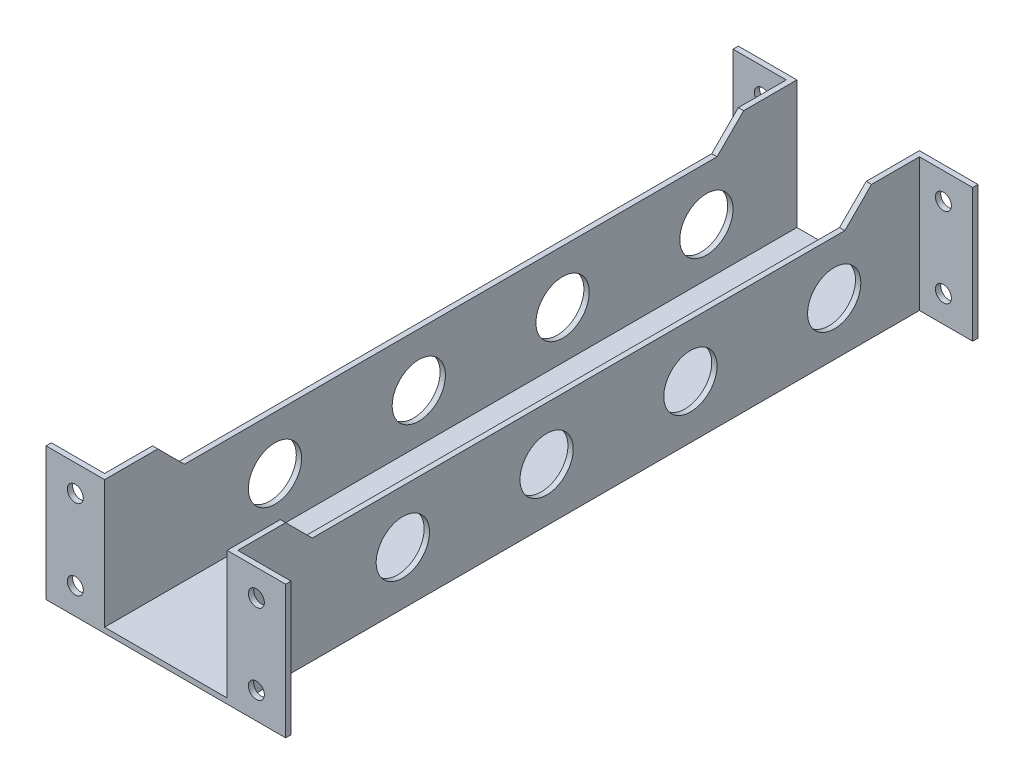
SolidWorks part; units mm, degrees
material "1060 Alloy"
ref_plane "Front Plane" through (0, 0, 0) normal (0, 0, 1) x (1, 0, 0)
ref_plane "Top Plane" through (0, 0, 0) normal (0, 1, 0) x (1, 0, 0)
ref_plane "Right Plane" through (0, 0, 0) normal (1, 0, 0) x (0, 0, -1)
sketch "Sketch1" plane through (0, 0, 0) normal (0, 1, 0) x (1, 0, 0)
  line L1 (-12.5, -65) -> (12.5, -65)
  line L2 (-12.5, -65) -> (-12.5, 65)
  line L3 (-12.5, 65) -> (12.5, 65)
  line L4 (12.5, -65) -> (12.5, 65)
  line L5 (-12.5, -65) -> (12.5, 65) construction
  line L6 (-12.5, 65) -> (12.5, -65) construction
  point P0 (0, 0)
  dimension "D1" = 130
  dimension "D2" = 25
extrude "Boss-Extrude1" add sketch "Sketch1" along normal blind 1
sketch "Sketch2" plane through (0, 1, 0) normal (0, 1, 0) x (1, 0, 0)
  line L0 (-12.5, -65) -> (12.5, -65) construction
  line L1 (12.5, 65) -> (11.5, 65)
  line L2 (12.5, 65) -> (12.5, -65)
  line L3 (12.5, -65) -> (11.5, -65)
  line L4 (11.5, 65) -> (11.5, -65)
  line L6 (-12.5, 65) -> (-11.5, 65)
  line L7 (-12.5, 65) -> (-12.5, -65)
  line L8 (-12.5, -65) -> (-11.5, -65)
  line L9 (-11.5, 65) -> (-11.5, -65)
  dimension "D1" = 1
  dimension "D2" = 1
extrude "Boss-Extrude2" add sketch "Sketch2" along normal blind 24
sketch "Sketch3" plane through (12.5, 0, 0) normal (1, 0, 0) x (0, 0, -1)
  line L0 (-65, 0) -> (65, 0) construction
  line L1 (-65, 25) -> (-64, 25)
  line L2 (-65, 25) -> (-65, 0)
  line L3 (-65, 0) -> (-64, 0)
  line L4 (-64, 25) -> (-64, 0)
  line L6 (65, 25) -> (64, 25)
  line L7 (65, 25) -> (65, 0)
  line L8 (65, 0) -> (64, 0)
  line L9 (64, 25) -> (64, 0)
  dimension "D1" = 1
  dimension "D2" = 1
extrude "Boss-Extrude3" add sketch "Sketch3" along normal blind 10
sketch "Sketch4" plane through (-12.5, 0, 0) normal (-1, 0, 0) x (0, 0, 1)
  line L0 (-65, 0) -> (65, 0) construction
  line L1 (-65, 25) -> (-64, 25)
  line L2 (-65, 25) -> (-65, 0)
  line L3 (-65, 0) -> (-64, 0)
  line L4 (-64, 25) -> (-64, 0)
  line L6 (65, 25) -> (64, 25)
  line L7 (65, 25) -> (65, 0)
  line L8 (65, 0) -> (64, 0)
  line L9 (64, 25) -> (64, 0)
  dimension "D1" = 1
  dimension "D2" = 1
extrude "Boss-Extrude4" add sketch "Sketch4" along normal blind 10
sketch "Sketch5" plane through (0, 1, 0) normal (0, 1, 0) x (1, 0, 0)
  line L0 (0, -65) -> (0, -38)
  line L1 (-11.5, -65) -> (11.5, -65) construction
  line L2 (0, -38) -> (0, -33)
  line L3 (0, -28) -> (0, -11)
  line L4 (0, -11) -> (0, -6)
  line L5 (0, -1) -> (0, 16)
  line L6 (0, 16) -> (0, 21)
  line L7 (0, 26) -> (0, 43)
  line L8 (0, 43) -> (0, 48)
  circle A0 centre (0, -33) radius 5
  circle A1 centre (0, -6) radius 5
  circle A2 centre (0, 21) radius 5
  circle A3 centre (0, 48) radius 5
  dimension "D1" = 27
  dimension "D2" = 5
  dimension "D3" = 17
  dimension "D4" = 5
  dimension "D5" = 17
  dimension "D6" = 5
  dimension "D7" = 17
  dimension "D8" = 5
extrude "Cut-Extrude1" cut sketch "Sketch5" against normal through all
sketch "Sketch10" plane through (0, 0, 65) normal (0, 0, 1) x (1, 0, 0)
  line L0 (17, 25) -> (17, 20)
  line L1 (11.5, 25) -> (22.5, 25) construction
  line L2 (17, 20) -> (22.5, 20)
  line L3 (22.5, 25) -> (22.5, 0) construction
  line L4 (17, 0) -> (17, 5)
  line L6 (-22.5, 0) -> (22.5, 0) construction
  line L7 (-17, 25) -> (-17, 20)
  line L8 (-22.5, 25) -> (-11.5, 25) construction
  circle A0 centre (17, 20) radius 1.5
  circle A1 centre (17, 5) radius 1.5
  circle A2 centre (-17, 20) radius 1.5
  circle A3 centre (-17, 5) radius 1.5
  dimension "D4" = 3
  dimension "D5" = 3
  dimension "D6" = 3
  dimension "D7" = 3
  dimension "D1" = 5
  dimension "D2" = 5
  dimension "D3" = 5
extrude "Cut-Extrude3" cut sketch "Sketch10" against normal through all
sketch "Sketch11" plane through (12.5, 0, 0) normal (1, 0, 0) x (0, 0, -1)
  line L0 (-65, 25) -> (-55, 25)
  line L1 (-64, 25) -> (64, 25) construction
  line L2 (-55, 25) -> (-50, 20)
  line L3 (-50, 20) -> (50, 20)
  line L4 (50, 20) -> (55, 25)
  line L5 (55, 25) -> (65, 25)
  line L6 (0, 25) -> (0, 20)
  line L7 (-55, 25) -> (55, 25)
  line M8 (64, 25) -> (-64, 25)
  dimension "D1" = 10
  dimension "D2" = 10
  dimension "D3" = 5
extrude "Cut-Extrude4" cut sketch "Sketch11" against normal through all and the other way through all contours L6 L2 L3 M8 | L6 L3 L4 M8
sketch "Sketch9" plane through (12.5, 0, 0) normal (1, 0, 0) x (0, 0, -1)
  line L0 (-21.4201, 0) -> (-21.4201, 10)
  line L2 (-38, 10) -> (-33, 10)
  line L3 (-28, 10) -> (-11, 10)
  line L4 (-11, 10) -> (-6, 10)
  line L5 (-1, 10) -> (16, 10)
  line L6 (16, 10) -> (21, 10)
  line L7 (26, 10) -> (43, 10)
  line L8 (43, 10) -> (48, 10)
  line L11 (-64, 0) -> (64, 0) construction
  line L12 (-38, 10) -> (-65, 10)
  line L14 (-65, 25) -> (-65, 0) construction
  circle A0 centre (-33, 10) radius 5
  circle A1 centre (-6, 10) radius 5
  circle A2 centre (21, 10) radius 5
  circle A3 centre (48, 10) radius 5
  dimension "D1" = 10
  dimension "D2" = 5
  dimension "D3" = 17
  dimension "D4" = 5
  dimension "D5" = 17
  dimension "D6" = 5
  dimension "D7" = 17
  dimension "D8" = 5
  dimension "D9" = 27
extrude "Cut-Extrude2" cut sketch "Sketch9" against normal through all
